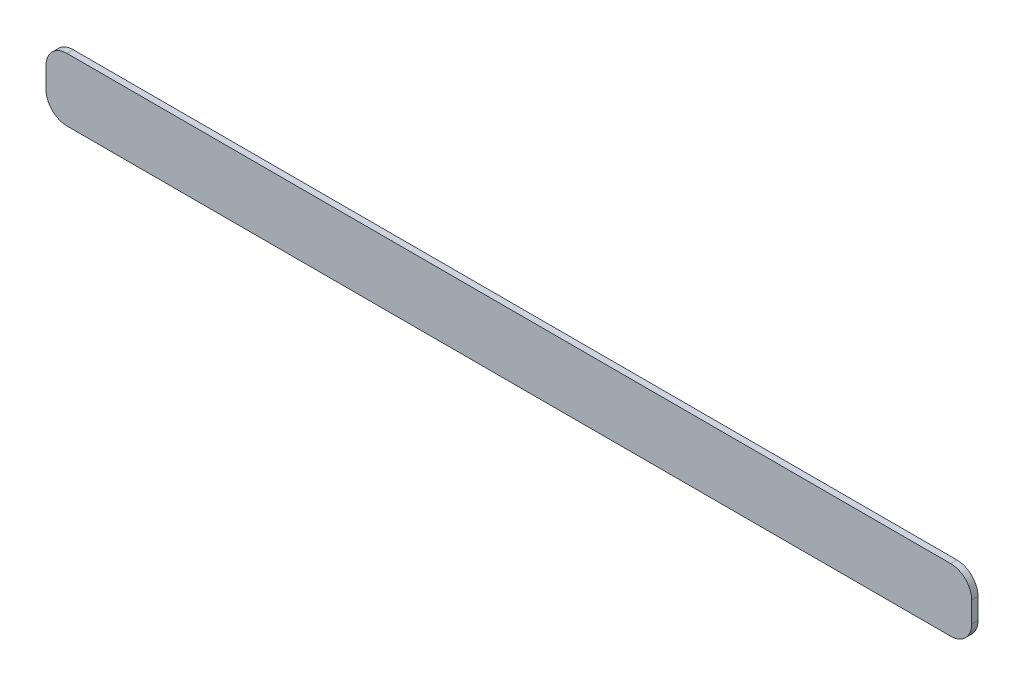
SolidWorks part; units mm, degrees
material "PMMA"
ref_plane "Plan de face" through (0, 0, 0) normal (0, 0, 1) x (1, 0, 0)
ref_plane "Plan de dessus" through (0, 0, 0) normal (0, 1, 0) x (1, 0, 0)
ref_plane "Plan de droite" through (0, 0, 0) normal (1, 0, 0) x (0, 0, -1)
sketch "Esquisse1" plane through (0, 0, 0) normal (0, 0, 1) x (1, 0, 0)
  line L1 (10, 0) -> (429.9, 0)
  line L2 (0, 10) -> (0, 19.9)
  line L3 (10, 29.9) -> (429.9, 29.9)
  line L4 (439.9, 10) -> (439.9, 19.9)
  arc A0 (429.9, 0) -> (439.9, 10) centre (429.9, 10) ccw
  arc A1 (439.9, 19.9) -> (429.9, 29.9) centre (429.9, 19.9) ccw
  arc A2 (0, 10) -> (10, 0) centre (10, 10) ccw
  arc A3 (0, 19.9) -> (10, 29.9) centre (10, 19.9) cw
  point P9 (439.9, 29.9)
  point P12 (0, 0)
  point P15 (0, 29.9)
  dimension "D3" = 10
  dimension "D1" = 439.9
  dimension "D2" = 29.9
extrude "Boss.-Extru.1" add sketch "Esquisse1" along normal blind 3
